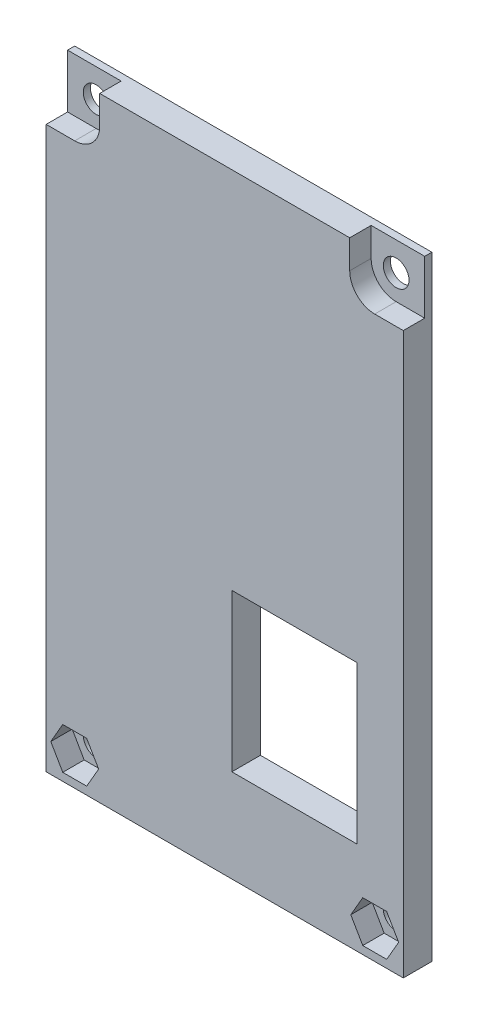
SolidWorks part; units mm, degrees
ref_plane "前视基准面" through (0, 0, 0) normal (0, 0, 1) x (1, 0, 0)
ref_plane "上视基准面" through (0, 0, 0) normal (0, 1, 0) x (1, 0, 0)
ref_plane "右视基准面" through (0, 0, 0) normal (1, 0, 0) x (0, 0, -1)
ref_plane "基准面4" through (0, 0, 0) normal (0, 0, -1) x (-1, 0, 0)
sketch "草图1" plane through (0, 0, 0) normal (0, 0, -1) x (-1, 0, 0)
  line L0 (-625, 343) -> (-625, 257)
  line L1 (-625, 257) -> (-575, 257)
  line L2 (-575, 257) -> (-575, 343)
  line L3 (-575, 343) -> (-625, 343)
extrude "凸台-拉伸1" add sketch "草图1" against normal blind 4
sketch "草图2" plane through (0, 0, 4) normal (0, 0, 1) x (1, 0, 0)
  line L0 (618.5, 270) -> (618.5, 292)
  line L1 (618.5, 292) -> (601, 292)
  line L2 (601, 292) -> (601, 270)
  line L3 (601, 270) -> (618.5, 270)
extrude "切除-拉伸1" cut sketch "草图2" against normal through all
sketch "草图3" plane through (0, 0, 4) normal (0, 0, 1) x (1, 0, 0)
  line L0 (580.675, 258.0988) -> (582.35, 261)
  line L1 (582.35, 261) -> (580.675, 263.9012)
  line L2 (580.675, 263.9012) -> (577.325, 263.9012)
  line L3 (577.325, 263.9012) -> (575.65, 261)
  line L4 (575.65, 261) -> (577.325, 258.0988)
  line L5 (577.325, 258.0988) -> (580.675, 258.0988)
extrude "切除-拉伸2" cut sketch "草图3" against normal blind 3
sketch "草图4" plane through (0, 343, 0) normal (0, 1, 0) x (-1, 0, 0)
  line L0 (-582.5, 4) -> (-582.5, 1)
  line L1 (-582.5, 1) -> (-575, 1)
  line L2 (-575, 1) -> (-575, 4)
  line L3 (-575, 4) -> (-582.5, 4)
extrude "切除-拉伸3" cut sketch "草图4" against normal blind 7.5
sketch "草图5" plane through (0, 343, 0) normal (0, 1, 0) x (-1, 0, 0)
  line L0 (-625, 4) -> (-625, 1)
  line L1 (-625, 1) -> (-617.5, 1)
  line L2 (-617.5, 1) -> (-617.5, 4)
  line L3 (-617.5, 4) -> (-625, 4)
extrude "切除-拉伸4" cut sketch "草图5" against normal blind 7.5
sketch "草图6" plane through (0, 0, 4) normal (0, 0, 1) x (1, 0, 0)
  line L0 (624.35, 261) -> (622.675, 263.9012)
  line L1 (622.675, 263.9012) -> (619.325, 263.9012)
  line L2 (619.325, 263.9012) -> (617.65, 261)
  line L3 (617.65, 261) -> (619.325, 258.0988)
  line L4 (619.325, 258.0988) -> (622.675, 258.0988)
  line L5 (622.675, 258.0988) -> (624.35, 261)
extrude "切除-拉伸5" cut sketch "草图6" against normal blind 3
hole_wizard "Ø3.6 (3.6) 直径孔1" positions "草图8" profile "草图7" hole size "Ø3.6" standard "ANSI Metric"
sketch "草图8" plane through (0, 0, 0) normal (0, 0, -1) x (-1, 0, 0)
  point P0 (-579, 339)
  point P1 (-621, 339)
  point P2 (-579, 261)
  point P3 (-621, 261)
sketch "草图7" plane through (579, 339, 0) normal (1, 0, 0) x (0, 1, 0)
  line L0 (0, 0) -> (0, 4)
  line L1 (0, 4) -> (1.8, 4)
  line L2 (1.8, 4) -> (1.8, 0)
  line L5 (1.8, 0) -> (0, 0)
  line L11 (0, -6.35) -> (0, 107.95) construction
  dimension "通孔孔直径" = 3.6
  dimension "通孔孔深度" = 4
fillet "圆角1" radius 3.5 2 edges at (582.5, 335.5, 2.5) (617.5, 335.5, 2.5)
